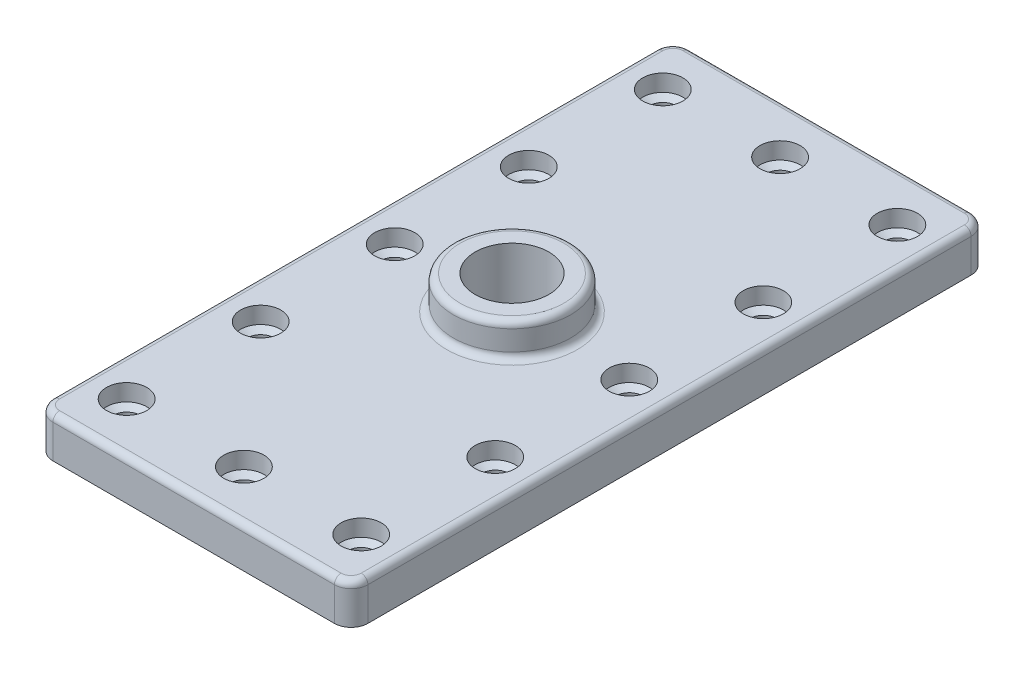
SolidWorks part; units mm, degrees
ref_plane "Front" through (0, 0, 0) normal (0, 0, 1) x (1, 0, 0)
ref_plane "Top" through (0, 0, 0) normal (0, 1, 0) x (1, 0, 0)
ref_plane "Right" through (0, 0, 0) normal (1, 0, 0) x (0, 0, -1)
sketch "Sketch1" plane through (0, 0, 0) normal (0, 1, 0) x (1, 0, 0)
  line L0 (-47, 95) -> (47, -95) construction
  line L1 (-47, -95) -> (47, -95)
  line L2 (-47, -95) -> (-47, 95)
  line L3 (-47, 95) -> (47, 95)
  line L4 (47, -95) -> (47, 95)
  dimension "D1" = 190
  dimension "D2" = 94
extrude "plate" add sketch "Sketch1" along normal blind 12
sketch "Sketch2" plane through (0, 12, 0) normal (0, 1, 0) x (-1, 0, 0)
  circle A0 centre (0, 0) radius 17.5
  dimension "D1" = 35
extrude "boss" add sketch "Sketch2" along normal blind 10
sketch "Sketch3" plane through (0, 22, 0) normal (0, 1, 0) x (-1, 0, 0)
  circle A0 centre (0, 0) radius 11
  dimension "D1" = 22
extrude "center hole" cut sketch "Sketch3" against normal through all
hole_wizard "pattern hole" positions "Sketch5" profile "Sketch4" legacy end condition through all
sketch "Sketch5" plane through (0, 12, 0) normal (0, 1, 0) x (-1, 0, 0)
  line L0 (47, 95) -> (-47, 95) construction
  line L1 (47, -95) -> (47, 95) construction
  point P0 (35, 80)
  dimension "D1" = 15
  dimension "D2" = 12
sketch "Sketch4" plane through (-35, 12, 80) normal (1, 0, 0) x (0, 0, 1)
  line L0 (0, 0) -> (0, 12)
  line L1 (0, 12) -> (4, 12)
  line L2 (4, 12) -> (4, 6.2017)
  line L3 (4, 6.2017) -> (6, 5)
  line L4 (6, 5) -> (6, 0)
  line L5 (6, 0) -> (0, 0)
  line L6 (0, -6.13) -> (0, 109.2824) construction
  line L7 (-4, 6.2017) -> (-6, 5) construction
  line L8 (0, 12) -> (-4, 12) construction
  dimension "Diameter" = 8
  dimension "Depth" = 12
  dimension "C-Drill Diameter" = 12
  dimension "C-Drill Depth" = 5
  dimension "C-Drill Angle" = 118
fillet "R5" radius 5 4 edges at (-47, 6, -95) (47, 6, -95) (47, 6, 95) (-47, 6, 95)
fillet "R2" radius 2 10 edges at (0, 12, -17.5) (0, 22, 17.5) (47, 12, 0) (0, 12, 95) (-47, 12, 0) (0, 12, -95) (45.5355, 12, -93.5355) (-45.5355, 12, -93.5355) (-45.5355, 12, 93.5355) (45.5355, 12, 93.5355)
pattern_linear "LPattern1" count 5 spacing 40 along (0, 0, -1) count 2 spacing 70 along (1, 0, 0) of "pattern hole"
pattern_linear "LPattern2" count 2 spacing 35 along (1, 0, 0) of "pattern hole"
pattern_linear "LPattern3" count 2 spacing 160 along (0, 0, -1) of "LPattern2"
